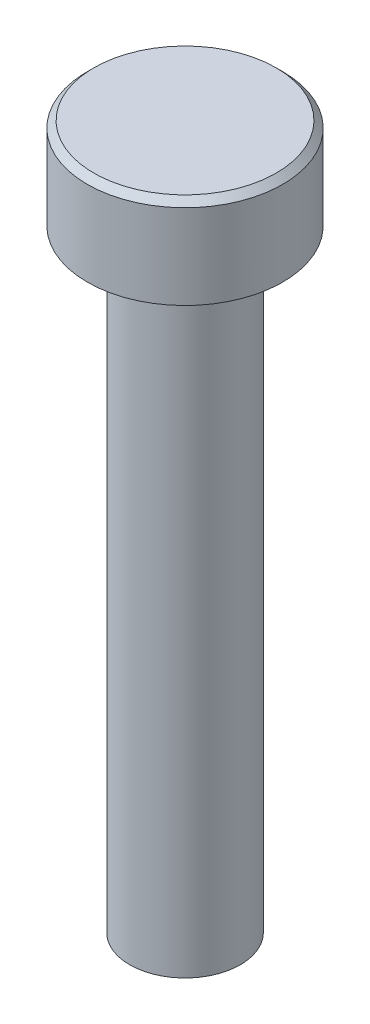
SolidWorks part; units mm, degrees
ref_plane "Спереди" through (0, 0, 0) normal (0, 0, 1) x (1, 0, 0)
ref_plane "Сверху" through (0, 0, 0) normal (0, 1, 0) x (1, 0, 0)
ref_plane "Справа" through (0, 0, 0) normal (1, 0, 0) x (0, 0, -1)
sketch "Эскиз1" plane through (0, 0, 0) normal (0, 0, 1) x (1, 0, 0)
  line L0 (0, 0) -> (0, -31.5767) construction
  line L1 (0, 0) -> (0, 108)
  line L2 (0, 108) -> (15, 108)
  line L3 (15, 108) -> (15, 94)
  line L4 (15, 94) -> (8.5, 94)
  line L5 (8.5, 94) -> (8.5, 0)
  line L6 (8.5, 0) -> (0, 0)
  dimension "D1" = 17
  dimension "D2" = 30
  dimension "D3" = 94
  dimension "D4" = 108
revolve "Повернуть1" add sketch "Эскиз1" angle 360 about L0
chamfer "Фаска1" distance 1 angle 45 1 edges at (0, 108, 15)
